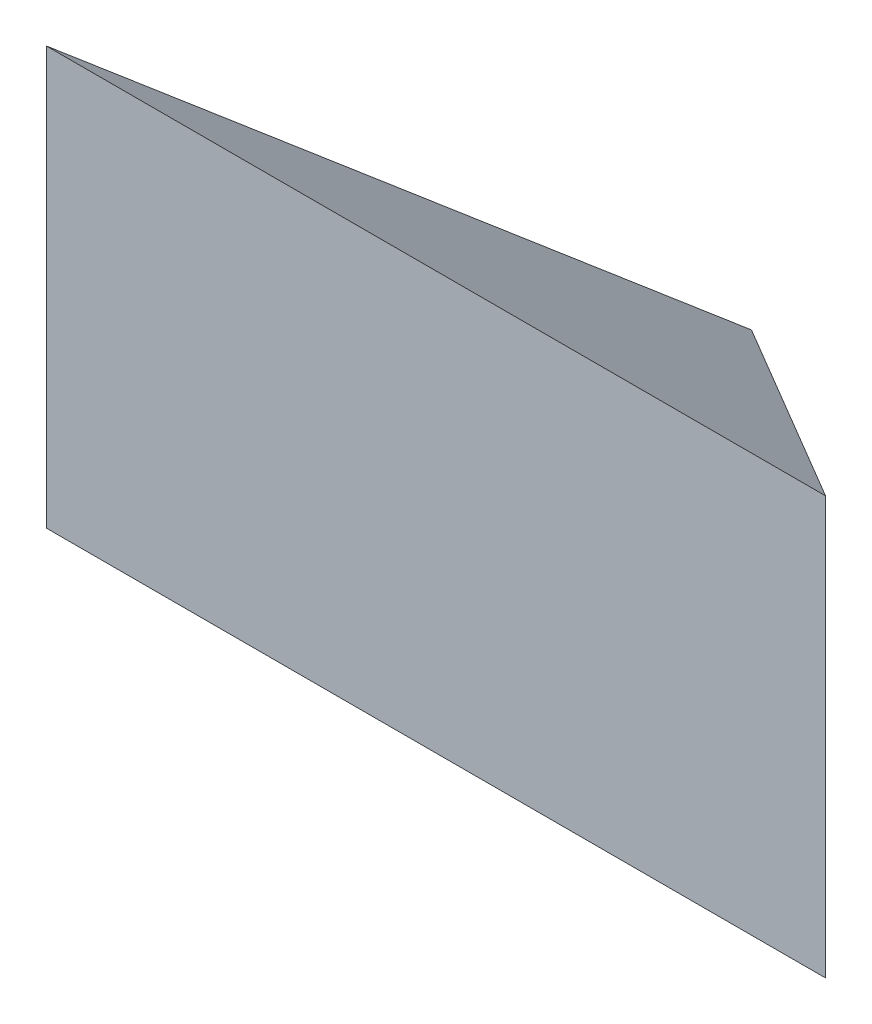
SolidWorks part; units mm, degrees
ref_plane "Front Plane" through (0, 0, 0) normal (0, 0, 1) x (1, 0, 0)
ref_plane "Top Plane" through (0, 0, 0) normal (0, 1, 0) x (1, 0, 0)
ref_plane "Right Plane" through (0, 0, 0) normal (1, 0, 0) x (0, 0, -1)
sketch3d "3DSketch1"
  line L0 (0, -5.2987, -130.8732) -> (0, -5.2987, -132.2982) construction
  line L1 (-1.5, -5.2987, -131.1496) -> (-1.5, -5.2987, -137.1496) construction
  line L2 (0, -5.2987, -132.2982) -> (0, 50.2997, -48.2982)
  line L3 (0, 50.2997, -48.2982) -> (0, -60.8971, -48.2982)
  line L4 (0, -60.8971, -48.2982) -> (0, -5.2987, -132.2982)
  line L5 (-103.7314, 50.2997, -48.2982) -> (103.7314, 50.2997, -48.2982)
  line L6 (-103.7314, -60.8971, -48.2982) -> (103.7314, -60.8971, -48.2982)
  line L7 (103.7314, 50.2997, -48.2982) -> (103.7314, -60.8971, -48.2982)
  line L8 (-103.7314, 50.2997, -48.2982) -> (-103.7314, -60.8971, -48.2982)
  line L9 (0, -5.2987, -132.2982) -> (-103.7314, -5.2987, -48.2982)
  line L10 (0, -5.2987, -132.2982) -> (103.7314, -5.2987, -48.2982)
  line L11 (103.7314, -5.2987, -48.2982) -> (-103.7314, -5.2987, -48.2982)
  point P7 (0, -5.2987, -48.2982)
  dimension "D1" = 1.425
  dimension "D2" = 67
  dimension "D3" = 84
  dimension "D4" = 102
extrude "Boss-Extrude1" add sketch "3DSketch1" along a picked direction on the side against the normal blind 90.1013 contours L6 L7 L5 L8
sketch "Sketch3" plane through (-103.7314, 0, 0) normal (-1, 0, 0) x (0, 0, 1)
  line L0 (-48.2982, 50.2997) -> (-132.2982, -5.2987)
  line L1 (-132.2982, -5.2987) -> (-48.2982, -60.8971)
  line L2 (-48.2982, -60.8971) -> (-138.3996, -60.8971)
  line L3 (-138.3996, -60.8971) -> (-138.3996, 50.2997)
  line L4 (-138.3996, 50.2997) -> (-48.2982, 50.2997)
sketch "Sketch2" plane through (0, 50.2997, 0) normal (0, 1, 0) x (1, 0, 0)
  line L0 (-103.7314, 48.2982) -> (0, 132.2982)
  line L1 (0, 132.2982) -> (103.7314, 48.2982)
  line L2 (-103.7314, 48.2982) -> (-103.7314, 138.3996)
  line L3 (-103.7314, 138.3996) -> (103.7314, 138.3996)
  line L4 (103.7314, 138.3996) -> (103.7314, 48.2982)
extrude "Cut-Extrude3" cut sketch "Sketch3" against normal through all
extrude "Cut-Extrude4" cut sketch "Sketch2" against normal through all
equation "\"D1@3DSketch1\"=2.85/2"
